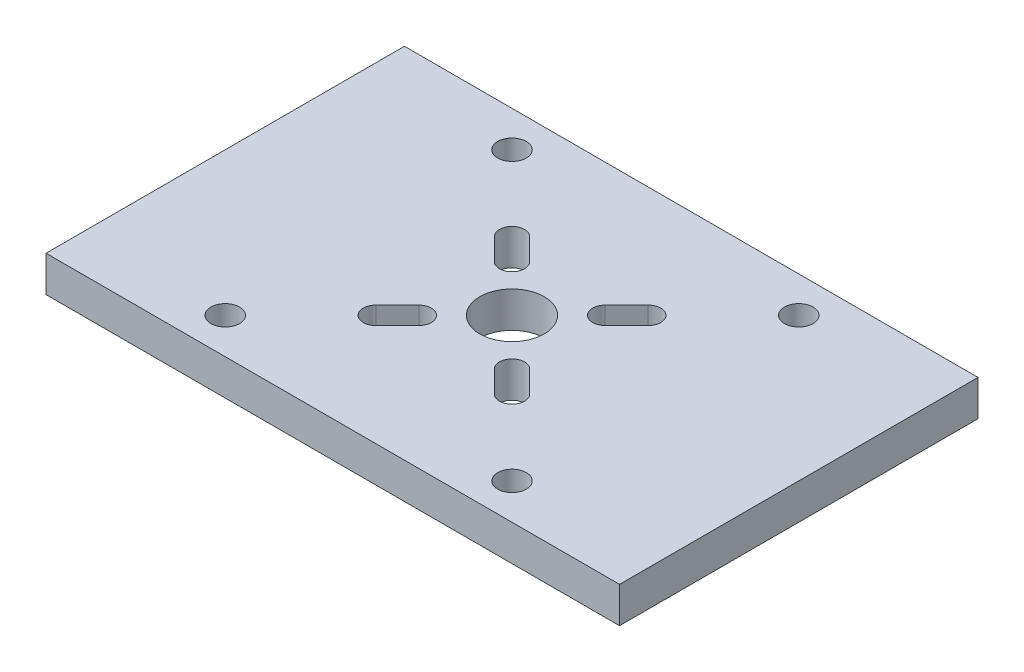
SolidWorks part; units mm, degrees
ref_plane "Front Plane" through (0, 0, 0) normal (0, 0, 1) x (1, 0, 0)
ref_plane "Top Plane" through (0, 0, 0) normal (0, 1, 0) x (1, 0, 0)
ref_plane "Right Plane" through (0, 0, 0) normal (1, 0, 0) x (0, 0, -1)
sketch "Sketch1" plane through (0, 0, 0) normal (0, 1, 0) x (1, 0, 0)
  line L1 (80, 50) -> (-80, 50)
  line L2 (80, 50) -> (80, -50)
  line L3 (80, -50) -> (-80, -50)
  line L4 (-80, 50) -> (-80, -50)
  line L5 (80, 50) -> (-80, -50) construction
  line L6 (80, -50) -> (-80, 50) construction
  point P0 (0, 0)
  dimension "D1" = 160
  dimension "D2" = 100
extrude "base" add sketch "Sketch1" along normal blind 10 contours L1 L4 L3 L2
sketch "Sketch2" plane through (0, 10, 0) normal (0, 1, 0) x (1, 0, 0)
  circle A0 centre (0, 0) radius 9
  dimension "D1" = 18
extrude "actuator cut" cut sketch "Sketch2" against normal blind 40
sketch "Sketch3" plane through (0, 10, 0) normal (0, 1, 0) x (1, 0, 0)
  line L0 (19, -19) -> (13, -13) construction
  line L1 (0, 0) -> (0, 19) construction
  line L2 (-19, -19) -> (19, 19) construction
  line L3 (-19, -19) -> (-13, -13) construction
  line L4 (-21.4749, -16.5251) -> (-15.4749, -10.5251)
  line L5 (-16.5251, -21.4749) -> (-10.5251, -15.4749)
  line L6 (21.4749, -16.5251) -> (15.4749, -10.5251)
  line L7 (16.5251, -21.4749) -> (10.5251, -15.4749)
  line L8 (0, 0) -> (19, 0) construction
  line L9 (19, 19) -> (13, 13) construction
  line L10 (21.4749, 16.5251) -> (15.4749, 10.5251)
  line L11 (16.5251, 21.4749) -> (10.5251, 15.4749)
  line L12 (-19, 19) -> (-13, 13) construction
  line L13 (-21.4749, 16.5251) -> (-15.4749, 10.5251)
  line L14 (-16.5251, 21.4749) -> (-10.5251, 15.4749)
  arc A4 (-21.4749, -16.5251) -> (-16.5251, -21.4749) centre (-19, -19) ccw
  arc A5 (-10.5251, -15.4749) -> (-15.4749, -10.5251) centre (-13, -13) ccw
  arc A6 (21.4749, -16.5251) -> (16.5251, -21.4749) centre (19, -19) cw
  arc A7 (10.5251, -15.4749) -> (15.4749, -10.5251) centre (13, -13) cw
  arc A8 (21.4749, 16.5251) -> (16.5251, 21.4749) centre (19, 19) ccw
  arc A9 (10.5251, 15.4749) -> (15.4749, 10.5251) centre (13, 13) ccw
  arc A10 (-21.4749, 16.5251) -> (-16.5251, 21.4749) centre (-19, 19) cw
  arc A11 (-10.5251, 15.4749) -> (-15.4749, 10.5251) centre (-13, 13) cw
  point P1 (-16, -16)
  point P10 (16, -16)
  point P20 (16, 16)
  point P27 (-16, 16)
  dimension "D5" = 3.5
  dimension "D4" = 19
  dimension "D1" = 13
  dimension "D2" = 19
  dimension "D3" = 45
  dimension "D6" = 19
extrude "Cut-Extrude1" cut sketch "Sketch3" against normal up to next
sketch "Sketch4" plane through (0, 0, 0) normal (0, -1, 0) x (1, 0, 0)
  line L0 (21.4749, 16.5251) -> (15.4749, 10.5251) construction
  line L1 (10.5251, 15.4749) -> (16.5251, 21.4749) construction
  line L2 (-15.4749, 10.5251) -> (-21.4749, 16.5251) construction
  line L3 (-16.5251, 21.4749) -> (-10.5251, 15.4749) construction
  line L4 (-10.5251, -15.4749) -> (-16.5251, -21.4749) construction
  line L5 (-21.4749, -16.5251) -> (-15.4749, -10.5251) construction
  line L6 (16.5251, -21.4749) -> (10.5251, -15.4749) construction
  line L7 (15.4749, -10.5251) -> (21.4749, -16.5251) construction
  line L8 (21.4749, 16.5251) -> (15.4749, 10.5251) construction
  line L9 (10.5251, 15.4749) -> (16.5251, 21.4749) construction
  line L10 (-15.4749, 10.5251) -> (-21.4749, 16.5251) construction
  line L11 (-16.5251, 21.4749) -> (-10.5251, 15.4749) construction
  line L12 (-10.5251, -15.4749) -> (-16.5251, -21.4749) construction
  line L13 (-21.4749, -16.5251) -> (-15.4749, -10.5251) construction
  line L14 (16.5251, -21.4749) -> (10.5251, -15.4749) construction
  line L15 (15.4749, -10.5251) -> (21.4749, -16.5251) construction
  line L16 (23.2426, 14.7574) -> (17.2426, 8.7574)
  line L17 (8.7574, 17.2426) -> (14.7574, 23.2426)
  line L18 (-17.2426, 8.7574) -> (-23.2426, 14.7574)
  line L19 (-14.7574, 23.2426) -> (-8.7574, 17.2426)
  line L20 (-8.7574, -17.2426) -> (-14.7574, -23.2426)
  line L21 (-23.2426, -14.7574) -> (-17.2426, -8.7574)
  line L22 (14.7574, -23.2426) -> (8.7574, -17.2426)
  line L23 (17.2426, -8.7574) -> (23.2426, -14.7574)
  arc A0 (10.5251, 15.4749) -> (15.4749, 10.5251) centre (13, 13) ccw construction
  arc A1 (21.4749, 16.5251) -> (16.5251, 21.4749) centre (19, 19) ccw construction
  arc A2 (-16.5251, 21.4749) -> (-21.4749, 16.5251) centre (-19, 19) ccw construction
  arc A3 (-15.4749, 10.5251) -> (-10.5251, 15.4749) centre (-13, 13) ccw construction
  arc A4 (-21.4749, -16.5251) -> (-16.5251, -21.4749) centre (-19, -19) ccw construction
  arc A5 (-10.5251, -15.4749) -> (-15.4749, -10.5251) centre (-13, -13) ccw construction
  arc A6 (15.4749, -10.5251) -> (10.5251, -15.4749) centre (13, -13) ccw construction
  arc A7 (16.5251, -21.4749) -> (21.4749, -16.5251) centre (19, -19) ccw construction
  arc A8 (10.5251, 15.4749) -> (15.4749, 10.5251) centre (13, 13) ccw construction
  arc A9 (21.4749, 16.5251) -> (16.5251, 21.4749) centre (19, 19) ccw construction
  arc A10 (-16.5251, 21.4749) -> (-21.4749, 16.5251) centre (-19, 19) ccw construction
  arc A11 (-15.4749, 10.5251) -> (-10.5251, 15.4749) centre (-13, 13) ccw construction
  arc A12 (-21.4749, -16.5251) -> (-16.5251, -21.4749) centre (-19, -19) ccw construction
  arc A13 (-10.5251, -15.4749) -> (-15.4749, -10.5251) centre (-13, -13) ccw construction
  arc A14 (15.4749, -10.5251) -> (10.5251, -15.4749) centre (13, -13) ccw construction
  arc A15 (16.5251, -21.4749) -> (21.4749, -16.5251) centre (19, -19) ccw construction
  arc A16 (8.7574, 17.2426) -> (17.2426, 8.7574) centre (13, 13) ccw
  arc A17 (23.2426, 14.7574) -> (14.7574, 23.2426) centre (19, 19) ccw
  arc A18 (-14.7574, 23.2426) -> (-23.2426, 14.7574) centre (-19, 19) ccw
  arc A19 (-17.2426, 8.7574) -> (-8.7574, 17.2426) centre (-13, 13) ccw
  arc A20 (-23.2426, -14.7574) -> (-14.7574, -23.2426) centre (-19, -19) ccw
  arc A21 (-8.7574, -17.2426) -> (-17.2426, -8.7574) centre (-13, -13) ccw
  arc A22 (17.2426, -8.7574) -> (8.7574, -17.2426) centre (13, -13) ccw
  arc A23 (14.7574, -23.2426) -> (23.2426, -14.7574) centre (19, -19) ccw
  dimension "D1" = 2.5
split line "Split Line1"
sketch "Sketch5" plane through (0, 10, 0) normal (0, 1, 0) x (1, 0, 0)
  line L0 (-40, 40) -> (-40, -40) construction
  line L1 (-40, -40) -> (40, -40) construction
  circle A0 centre (-40, -40) radius 3
  circle A1 centre (-40, 40) radius 3
  circle A2 centre (40, -40) radius 3
  circle A3 centre (40, 40) radius 3
  point P8 (-40, 0)
  point P9 (0, -40)
  dimension "D3" = 6
  dimension "D1" = 80
  dimension "D2" = 80
extrude "Cut-Extrude2" cut sketch "Sketch5" against normal up to next
sketch "Sketch6" plane through (0, 0, 0) normal (0, -1, 0) x (1, 0, 0)
  circle A0 centre (-40, 40) radius 4
  circle A1 centre (40, 40) radius 4
  circle A2 centre (40, -40) radius 4
  circle A3 centre (-40, -40) radius 4
  dimension "D1" = 8
extrude "Cut-Extrude3" cut sketch "Sketch6" against normal through all
equation "\"D4@Sketch3\"=\"D2@Sketch3\""
equation "\"D6@Sketch3\"=\"D2@Sketch3\""
